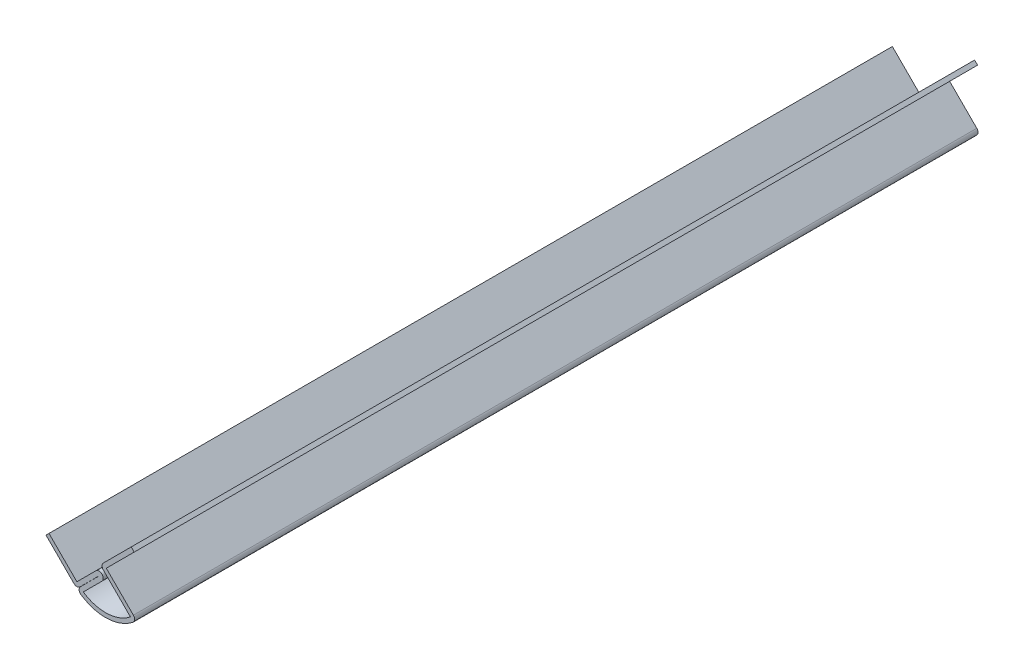
SolidWorks part; units mm, degrees
ref_plane "Front Plane" through (0, 0, 0) normal (0, 0, 1) x (1, 0, 0)
ref_plane "Top Plane" through (0, 0, 0) normal (0, 1, 0) x (1, 0, 0)
ref_plane "Right Plane" through (0, 0, 0) normal (1, 0, 0) x (0, 0, -1)
sketch "Sketch2" plane through (0, 0, 0) normal (0, 0, 1) x (1, 0, 0)
  line L0 (7.723, 7.723) -> (-6.7352, -6.7352) construction
  line L1 (0, 0) -> (0, -9.2315) construction
  line L2 (0, 0) -> (9.9899, -9.9899) construction
  line L3 (-6.7352, -6.7352) -> (-13.4704, 0)
  line L4 (-6.7352, -6.7352) -> (-2.1306, -2.1306)
  line L5 (-0.6758, -3.5854) -> (-5.182, -8.0916)
  line L6 (6.1825, -7.6193) -> (-1.0776, -0.3592)
  line L7 (-1.0776, -0.3592) -> (6.376, 7.0944)
  line L8 (0.3592, -0.3592) -> (7.0944, 6.376)
  line L9 (7.6557, -7.6557) -> (0.3592, -0.3592)
  line L10 (-1.3942, -2.8669) -> (-6.7172, -8.19)
  line L11 (-6.7352, -8.172) -> (-1.4121, -2.849)
  line L12 (-6.7352, -8.172) -> (-14.1888, -0.7184)
  line L13 (6.376, 7.0944) -> (7.0944, 6.376)
  line L14 (-14.1888, -0.7184) -> (-13.4704, 0)
  line L15 (-6.7352, -8.172) -> (-6.7172, -8.19) construction
  arc A0 (-2.1306, -2.1306) -> (-0.6758, -3.5854) centre (-1.4032, -2.858) cw
  arc A1 (-5.182, -8.0916) -> (6.1825, -7.6193) centre (0.1829, -0.2213) ccw
  arc A2 (-6.7172, -8.19) -> (7.6557, -7.6557) centre (0.1829, -0.2213) ccw
  arc A3 (-1.4121, -2.849) -> (-1.3942, -2.8669) centre (-1.4032, -2.858) cw
  dimension "D11" = 10.541
  dimension "D1" = 9.525
  dimension "D2" = 45
  dimension "D3" = 45
  dimension "D4" = 9.525
  dimension "D5" = 7.5406
  dimension "D6" = 2.0574
  dimension "D7" = 1.016
  dimension "D8" = 1.016
  dimension "D10" = 9.525
  dimension "D12" = 10.3187
  dimension "D9" = 1.016
extrude "Boss-Extrude1" add sketch "Sketch2" against normal blind 203.5175
fillet "Fillet1" radius 1.016 4 edges at (-6.7352, -8.172, -101.7587) (-6.7172, -8.19, -101.7587) (-1.0776, -0.3592, -101.7587) (7.6557, -7.6557, -101.7587)
